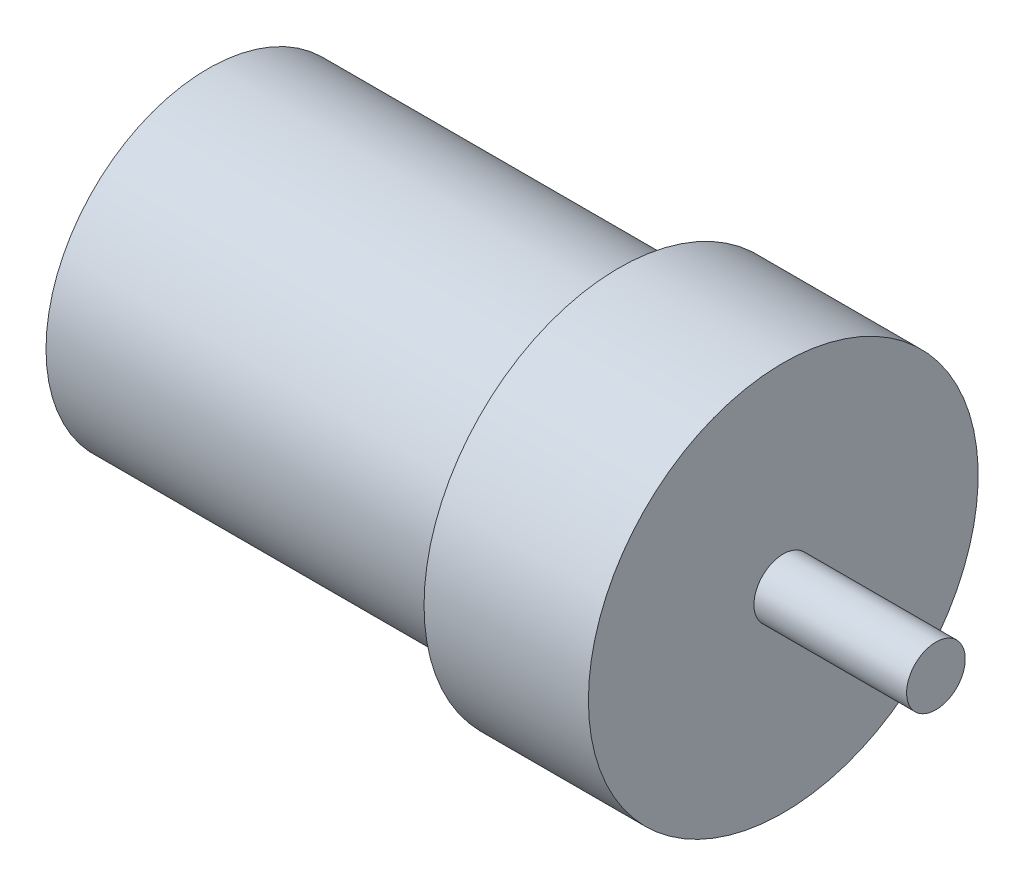
SolidWorks part; units mm, degrees
ref_plane "Front Plane" through (0, 0, 0) normal (0, 0, 1) x (1, 0, 0)
ref_plane "Top Plane" through (0, 0, 0) normal (0, 1, 0) x (1, 0, 0)
ref_plane "Right Plane" through (0, 0, 0) normal (1, 0, 0) x (0, 0, -1)
sketch "Sketch1" plane through (0, 0, 0) normal (0, 0, 1) x (1, 0, 0)
  line L0 (0, 53.4319) -> (0, 9.525) construction
  line L1 (-31.8127, 0) -> (0, 0) construction
  line L2 (0, 9.525) -> (0, 17.526)
  line L3 (0, 17.526) -> (44.45, 17.526)
  line L4 (44.45, 17.526) -> (44.45, 21.082)
  line L5 (44.45, 21.082) -> (62.23, 21.082)
  line L6 (62.23, 21.082) -> (62.23, 3.175)
  line L7 (62.23, 3.175) -> (78.74, 3.175)
  line L8 (78.74, 3.175) -> (78.74, 0)
  line L9 (78.74, 0) -> (45.72, 0)
  line L10 (0, 9.525) -> (45.72, 9.525)
  line L11 (45.72, 9.525) -> (45.72, 0)
  line L12 (0, 0) -> (0, -50.0714) construction
  line L13 (45.72, 0) -> (96.8916, 0) construction
  dimension "D1" = 35.052
  dimension "D2" = 42.164
  dimension "D3" = 6.35
  dimension "D4" = 16.51
  dimension "D5" = 44.45
  dimension "D6" = 17.78
  dimension "D7" = 19.05
  dimension "D8" = 45.72
revolve "Revolve1" add sketch "Sketch1" angle 360 about L1
